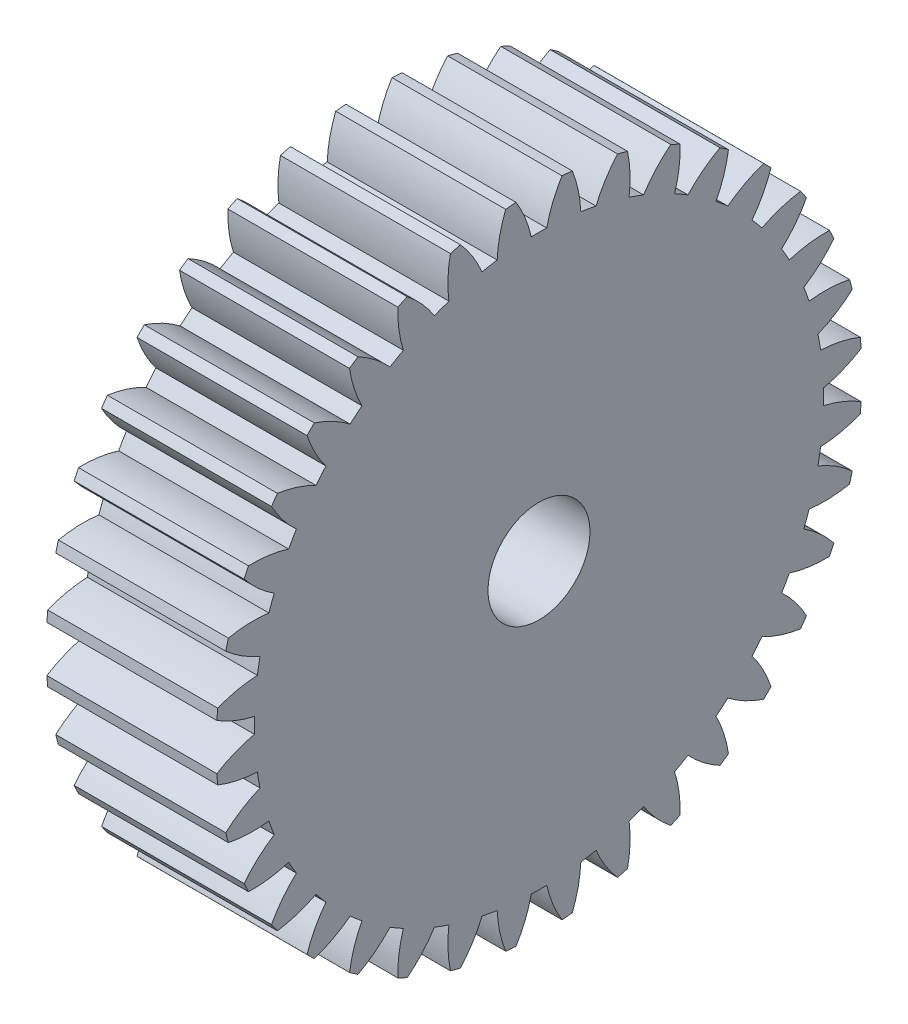
SolidWorks part; units mm, degrees
ref_plane "Plane1" through (0, 0, 0) normal (0, 0, 1) x (1, 0, 0)
ref_plane "Plane2" through (0, 0, 0) normal (0, 1, 0) x (1, 0, 0)
ref_plane "Plane3" through (0, 0, 0) normal (1, 0, 0) x (0, 0, -1)
other "Configuration Table"
sketch "HoldingSke" plane through (0, 0, 0) normal (0, 1, 0) x (1, 0, 0)
  line L0 (0, 0) -> (0.809, -0.5878)
  line L1 (-15, 0) -> (100, 0) construction
  line L2 (0, 0) -> (-2.1039, 2.3779)
  line L3 (0, 0) -> (-11.863, 4.5341)
  line L4 (0, 0) -> (6.9867, 5.0761)
  line L5 (0, 0) -> (-46.8476, -17.4728)
  line L6 (0, 0) -> (-8.2896, -5.593)
  line L7 (-2.1039, 2.3779) -> (8.6586, 51.2059)
  line L8 (-76.2, 54.61) -> (-75.3, 54.61)
  line L9 (-71.009, 38.7566) -> (-53.1078, 45.2721)
  line L10 (-76.2, 71.12) -> (104.1128, 71.12)
  line L11 (0, 0) -> (-10, 0)
  line L12 (-76.2, 101.6) -> (-76.162, 101.6)
  line L13 (24.9733, 27.94) -> (52.9518, 28.4284)
  line L14 (24.9733, 27.94) -> (24.9743, 27.94)
  line L15 (24.9733, 27.94) -> (100.4006, 29.5858)
  line L16 (-63.627, -1) -> (-12.827, -1)
  circle A0 centre (0, 0) radius 2.5
  circle A1 centre (0, 0) radius 16.749
  circle A2 centre (0, 0) radius 37.5
  circle A3 centre (0, 0) radius 2.5
  dimension "MHD" = 33.498
  dimension "Hub_dia" = 75
  dimension "Bore" = 5
  dimension "MBD" = 5
  dimension "Num_teeth" = 36
  dimension "Pitch" = 1
  dimension "Overall_len" = 50
  dimension "Show_teeth" = 36
  dimension "Thickness" = 10
  dimension "OAL" = 50.0001
  dimension "T_dim" = 0.9
  dimension "Ap" = 20
  dimension "H" = 19.05
  dimension "Pitch_radius" = 180.3128
  dimension "Width" = 10
  dimension "Backlash" = 0.038
  dimension "Addendum_fac" = 1
  dimension "Dedendum_fac" = 1.25
  dimension "Clearance_fac" = 0.25
  dimension "Dedendum_add" = 0.001
  dimension "Module" = 1
sketch "BasProSke" plane through (0, 0, 0) normal (0, 1, 0) x (1, 0, 0)
  line L0 (-10, 0) -> (60, 0) construction
  line L1 (0, 0) -> (0, 19)
  line L2 (0, 0) -> (10, 0)
  line L3 (10, 0) -> (10, 19)
  line L4 (10, 19) -> (0, 19)
  dimension "Thickness" = 10
  dimension "Diameter" = 38
revolve "Base-Revolve" add sketch "BasProSke" angle 360 about L0
sketch "TooCutSke" plane through (0, 0, 0) normal (1, 0, 0) x (0, 0, -1)
  line L1 (0, 0) -> (0, 107) construction
  line L2 (0, 0) -> (-0.8516, 17.9798) construction
  line L3 (0, 0) -> (-3.1351, 35.8344) construction
  line L4 (-0.8516, 17.9798) -> (-1.5676, 17.9172) construction
  arc A0 (0.4547, 16.7428) -> (-0.4547, 16.7428) centre (0, 0) ccw
  arc A1 (1.3689, 18.9761) -> (-1.3689, 18.9761) centre (0, 0) ccw
  circle A2 centre (0, 0) radius 18 construction
  circle A3 centre (0, 0) radius 16.9145 construction
  arc A4 (-0.4547, 16.7428) -> (-1.3689, 18.9761) centre (-7.4808, 15.1702) ccw
  arc A5 (1.3689, 18.9761) -> (0.4547, 16.7428) centre (7.4808, 15.1702) ccw
  dimension "Root_dia" = 33.498
  dimension "Overcut_dia" = 38.0508
  dimension "Pitch_dia" = 36
  dimension "Base_dia" = 33.8289
  dimension "Flank_rad" = 7.2
  dimension "Half_ang" = 5
  dimension "Half_CT" = 0.7186
extrude "ToothCut" cut sketch "TooCutSke" along normal through all
fillet "Breaks" [suppressed] radius 0.02
fillet "RootFillets" [suppressed] radius 0.251
pattern_circular "TeethCuts" count 36 every 10 about axis through (-10, 0, 0) along (1, 0, 0) of "ToothCut", "RootFillets", "Breaks"
sketch "HubNeaOneSke" plane through (0, 0, 0) normal (-1, 0, 0) x (0, 0, 1)
  circle A0 centre (0, 0) radius 16.749
  dimension "Diameter" = 33.498
extrude "HubNearOne" [suppressed] add sketch "HubNeaOneSke" along normal blind 40.0001
sketch "HubNeaBotSke" plane through (0, 0, 0) normal (-1, 0, 0) x (0, 0, 1)
  circle A0 centre (0, 0) radius 16.749
  dimension "Diameter" = 33.498
extrude "HubNearBoth" [suppressed] add sketch "HubNeaBotSke" along normal blind 20
ref_plane "FarPln" through (10, 0, 0) normal (1, 0, 0) x (0, 0, -1)
sketch "HubFarSke" plane through (10, 0, 0) normal (1, 0, 0) x (0, 0, -1)
  circle A0 centre (0, 0) radius 16.749
  dimension "Diameter" = 33.498
extrude "HubFar" [suppressed] add sketch "HubFarSke" along normal blind 20
sketch "BorSke" plane through (0, 0, 0) normal (1, 0, 0) x (0, 0, -1)
  circle A0 centre (0, 0) radius 2.5
  dimension "Diameter" = 5
extrude "Bore" cut sketch "BorSke" along normal mid plane 100.0001
sketch "KeySke" plane through (0, 0, 0) normal (1, 0, 0) x (0, 0, -1)
  line L0 (-1, 0) -> (-1, 3.4)
  line L1 (-1, 3.4) -> (1, 3.4)
  line L2 (1, 3.4) -> (1, 0)
  line L3 (0, 0) -> (0, 34) construction
  line L4 (-1, 0) -> (1, 0)
  dimension "Offset" = 3.4
  dimension "Width" = 2
extrude "Keyway" [suppressed] cut sketch "KeySke" along normal mid plane 100.0001
pattern_circular "Keyway2" [suppressed] count 2 every 90 about axis through (-10, 0, 0) along (1, 0, 0)
sketch "Sketch1" plane through (10, 0, 0) normal (1, 0, 0) x (0, 0, -1)
  circle A0 centre (0, 0) radius 3
  dimension "D1" = 6
extrude "Cut-Extrude1" cut sketch "Sketch1" against normal through all
equation "' \"Module@HoldingSke\" = 6.35"
equation "' \"Num_teeth@HoldingSke\" = 12"
equation "' \"Ap@HoldingSke\" =  20"
equation "' \"Ap@HoldingSke\" = 20"
equation "' \"Width@HoldingSke\" = 0.5 * 25.4"
equation "' \"Hub_dia@HoldingSke\"= 1 * 25.4"
equation "' \"Hub_dia@HoldingSke\" = 1 * 25.4"
equation "' \"Overall_len@HoldingSke\" = 1.0 * 25.4"
equation "' \"Bore@HoldingSke\" = 0.75 * 25.4"
equation "' \"T_dim@HoldingSke\" = 0.1 * 25.4"
equation "' \"Width@KeySke\" = 0.25 * 25.4"
equation "' \"Show_teeth@HoldingSke\" = 13"
equation "' \"Backlash@HoldingSke\" = 0.009 * 25.4"
equation "' \"Addendum_fac@HoldingSke\" = 1.0"
equation "' \"Dedendum_fac@HoldingSke\" = 1.25"
equation "' \"Dedendum_add@HoldingSke\" = 0.00005 * 25.4"
equation "' \"Clearance_fac@HoldingSke\" = 0.25"
equation "\"Pitch@HoldingSke\" = 1 / \"Module@HoldingSke\""
equation "\"Overcut_dia@TooCutSke\" = (\"Num_teeth@HoldingSke\" + 2 * \"Addendum_fac@HoldingSke\") / \"Pitch@HoldingSke\" + 0.002 * 25.4"
equation "\"Pitch_dia@TooCutSke\" = \"Num_teeth@HoldingSke\" / \"Pitch@HoldingSke\""
equation "\"Base_dia@TooCutSke\" = \"Num_teeth@HoldingSke\" / \"Pitch@HoldingSke\" * cos((\"Ap@HoldingSke\"  * 3.14159265 / 180))"
equation "\"Root_dia@TooCutSke\" = (\"Num_teeth@HoldingSke\" + 2) / \"Pitch@HoldingSke\" - 2 * (\"Addendum_fac@HoldingSke\" + \"Dedendum_fac@HoldingSke\") / \"Pitch@HoldingSke\" - \"Dedendum_add@HoldingSke\" * 2"
equation "\"Half_ang@TooCutSke\" = 180 / \"Num_teeth@HoldingSke\""
equation "\"Half_CT@TooCutSke\" = \"Num_teeth@HoldingSke\" / \"Pitch@HoldingSke\" * sin((3.14159265 / 2 / \"Num_teeth@HoldingSke\")) / 2 - 7 * \"Backlash@HoldingSke\" / 4"
equation "\"Flank_rad@TooCutSke\" = \"Num_teeth@HoldingSke\" / \"Pitch@HoldingSke\" / 5"
equation "\"Radius@RootFillets\" = \"Clearance_fac@HoldingSke\" / \"Pitch@HoldingSke\" + \"Dedendum_add@HoldingSke\""
equation "\"Break_rad@Breaks\" = 0.02 / \"Pitch@HoldingSke\""
equation "\"Thickness@HoldingSke\" = \"Width@HoldingSke\""
equation "\"OAL@HoldingSke\" = \"Thickness@HoldingSke\""
equation "\"MHD@HoldingSke\" = (\"Num_teeth@HoldingSke\" + 2) / \"Pitch@HoldingSke\" - 2 * (\"Addendum_fac@HoldingSke\" + \"Dedendum_fac@HoldingSke\")  / \"Pitch@HoldingSke\" - \"Dedendum_add@HoldingSke\" * 2"
equation "\"MBD@HoldingSke\" = (\"Num_teeth@HoldingSke\" + 2) / \"Pitch@HoldingSke\" - 2 * (\"Addendum_fac@HoldingSke\" + \"Dedendum_fac@HoldingSke\")  / \"Pitch@HoldingSke\" - \"Dedendum_add@HoldingSke\" * 2 - 0.002 * 25.4"
equation "\"MHD@HoldingSke\" = ((sgn( \"MHD@HoldingSke\" - \"Hub_dia@HoldingSke\" )-1)*( \"MHD@HoldingSke\" - \"Hub_dia@HoldingSke\" ))/-2+ \"Hub_dia@HoldingSke\""
equation "\"MBD@HoldingSke\" = ((sgn( \"MBD@HoldingSke\" - \"Bore@HoldingSke\" )-1)*( \"MBD@HoldingSke\" - \"Bore@HoldingSke\" ))/-2+ \"Bore@HoldingSke\""
equation "\"OAL@HoldingSke\" = ((sgn( \"OAL@HoldingSke\" - \"Overall_len@HoldingSke\" )+1)*( \"OAL@HoldingSke\" - \"Overall_len@HoldingSke\" ))/2 + \"Overall_len@HoldingSke\" + 0.000002 * 25.4"
equation "\"Num_teeth@TeethCuts\" = int( \"Show_teeth@HoldingSke\" ) + 1"
equation "\"Num_teeth@TeethCuts\" = ((sgn( \"Num_teeth@TeethCuts\" - \"Num_teeth@HoldingSke\" )-1)*( \"Num_teeth@TeethCuts\" - \"Num_teeth@HoldingSke\" ))/-2+ \"Num_teeth@HoldingSke\""
equation "\"Num_teeth@TeethCuts\" = ((sgn( \"Num_teeth@TeethCuts\" - 2.0)+1)*( \"Num_teeth@TeethCuts\" - 2.0))/2 +2.0"
equation "\"Angle@TeethCuts\" = 360.0 / \"Num_teeth@HoldingSke\""
equation "\"Diameter@BasProSke\" = (\"Num_teeth@HoldingSke\" + 2 * \"Addendum_fac@HoldingSke\") / \"Pitch@HoldingSke\""
equation "\"Thickness@BasProSke\"  = \"Thickness@HoldingSke\""
equation "' \"Fillet_rad@BasProSke\" =  \"Thickness@HoldingSke\" * 0.05"
equation "' \"Fillet_rad@BasProSke\" = \"Thickness@HoldingSke\" * 0.05"
equation "\"MHD@HoldingSke\" = ((sgn( \"MHD@HoldingSke\" - \"Root_dia@TooCutSke\" )-1)*( \"MHD@HoldingSke\" - \"Root_dia@TooCutSke\" ))/-2+ \"Root_dia@TooCutSke\""
equation "\"Diameter@HubNeaOneSke\" = \"MHD@HoldingSke\""
equation "\"Length@HubNearOne\" = \"OAL@HoldingSke\" - \"Thickness@BasProSke\""
equation "\"Diameter@HubNeaBotSke\" = \"MHD@HoldingSke\""
equation "\"Length@HubNearBoth\" = ( \"OAL@HoldingSke\" - \"Thickness@BasProSke\" ) / 2.0"
equation "\"Thickness@FarPln\" = \"Thickness@BasProSke\""
equation "\"Diameter@HubFarSke\" = \"MHD@HoldingSke\""
equation "\"Length@HubFar\" = ( \"OAL@HoldingSke\" - \"Thickness@BasProSke\" ) / 2.0"
equation "\"Diameter@BorSke\" = \"MBD@HoldingSke\""
equation "\"D1@Bore\" = \"OAL@HoldingSke\" * 2.0"
equation "\"D1@Keyway\" = \"OAL@HoldingSke\" * 2.0"
equation "\"Offset@KeySke\" = \"T_dim@HoldingSke\" + \"MBD@HoldingSke\" / 2.0"
